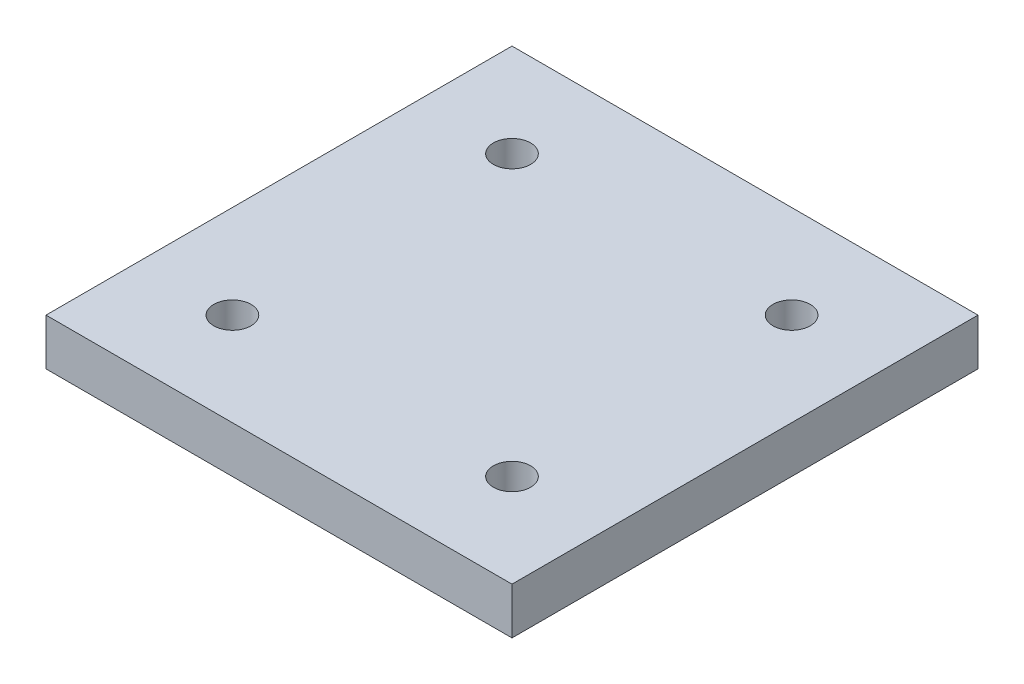
SolidWorks part; units mm, degrees
ref_plane "Спереди" through (0, 0, 0) normal (0, 0, 1) x (1, 0, 0)
ref_plane "Сверху" through (0, 0, 0) normal (0, 1, 0) x (1, 0, 0)
ref_plane "Справа" through (0, 0, 0) normal (1, 0, 0) x (0, 0, -1)
sketch "Эскиз1" plane through (0, 0, 0) normal (0, 1, 0) x (1, 0, 0)
  line L1 (-50, -50) -> (50, -50)
  line L2 (-50, -50) -> (-50, 50)
  line L3 (-50, 50) -> (50, 50)
  line L4 (50, -50) -> (50, 50)
extrude "Бобышка-Вытянуть1" add sketch "Эскиз1" along normal blind 10
sketch "Эскиз2" plane through (0, 10, 0) normal (0, 1, 0) x (1, 0, 0)
  line L0 (-50, 50) -> (50, -50) construction
  line L1 (50, 50) -> (-50, -50) construction
  circle A0 centre (-30, 30) radius 4
  circle A1 centre (30, 30) radius 4
  circle A2 centre (-30, -30) radius 4
  circle A3 centre (30, -30) radius 4
  point P8 (0, 0)
  point P20 (0, 0)
  point P25 (0, 0)
  dimension "D1" = 4
extrude "Вырез-Вытянуть1" cut sketch "Эскиз2" against normal through all
